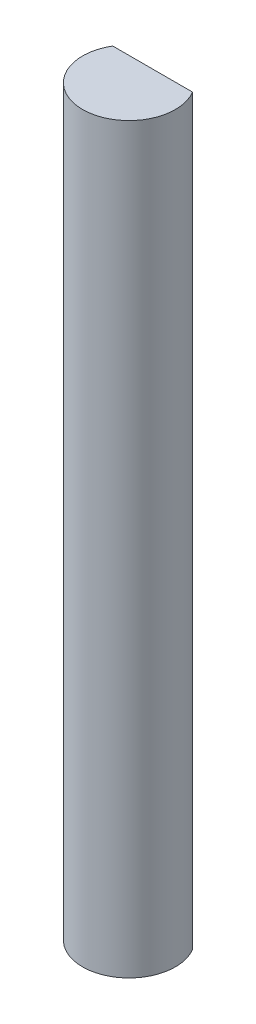
SolidWorks part; units mm, degrees
ref_plane "Front Plane" through (0, 0, 0) normal (0, 0, 1) x (1, 0, 0)
ref_plane "Top Plane" through (0, 0, 0) normal (0, 1, 0) x (1, 0, 0)
ref_plane "Right Plane" through (0, 0, 0) normal (1, 0, 0) x (0, 0, -1)
sketch "Sketch1" plane through (0, 0, 0) normal (0, 1, 0) x (1, 0, 0)
  line L0 (-2.7309, 1.6195) -> (2.7309, 1.6195)
  circle A0 centre (0, 0) radius 3.175
  dimension "D1" = 6.35
  dimension "D2" = 1.6195
extrude "Boss-Extrude1" add sketch "Sketch1" along normal blind 50.8 contours L0 A0
